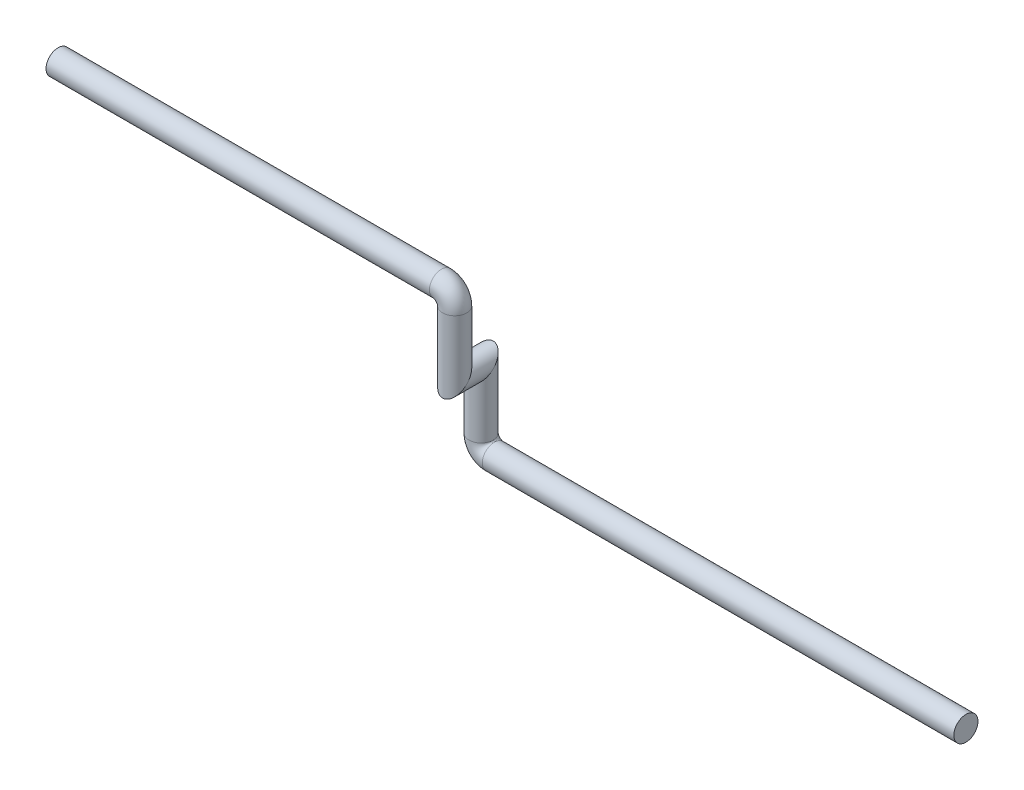
SolidWorks part; units mm, degrees
ref_plane "Alzado" through (0, 0, 0) normal (0, 0, 1) x (1, 0, 0)
ref_plane "Planta" through (0, 0, 0) normal (0, 1, 0) x (1, 0, 0)
ref_plane "Vista lateral" through (0, 0, 0) normal (1, 0, 0) x (0, 0, -1)
sketch3d "Croquis3D1"
  line L0 (0, 0, 0) -> (-535, 0, 0)
  line L1 (-550, 15, 0) -> (-550, 85, 0)
  line L3 (-550, 85, 0) -> (-550, 85, 30)
  line L4 (-550, 85, 30) -> (-550, 155, 30)
  line L5 (-565, 170, 30) -> (-1000, 170, 30)
  arc A0 (-550, 155, 30) -> (-565, 170, 30) centre (-565, 155, 30) ccw
  arc A1 (-535, 0, 0) -> (-550, 15, 0) centre (-535, 15, 0) ccw
  point P9 (-550, 170, 30)
  point P10 (-565, 155, 45)
  point P13 (-550, 0, 0)
  point P14 (-535, 15, -15)
  dimension "D2" = 15
  dimension "D1" = 550
  dimension "D4" = 30
  dimension "D5" = 85
  dimension "D6" = 450
sketch "Croquis1" plane through (0, 0, 0) normal (1, 0, 0) x (0, 0, -1)
  circle A0 centre (0, 0) radius 13.7
  dimension "D1" = 27.4
sweep "Barrer1" add profiles "Croquis1" path "Croquis3D1"
